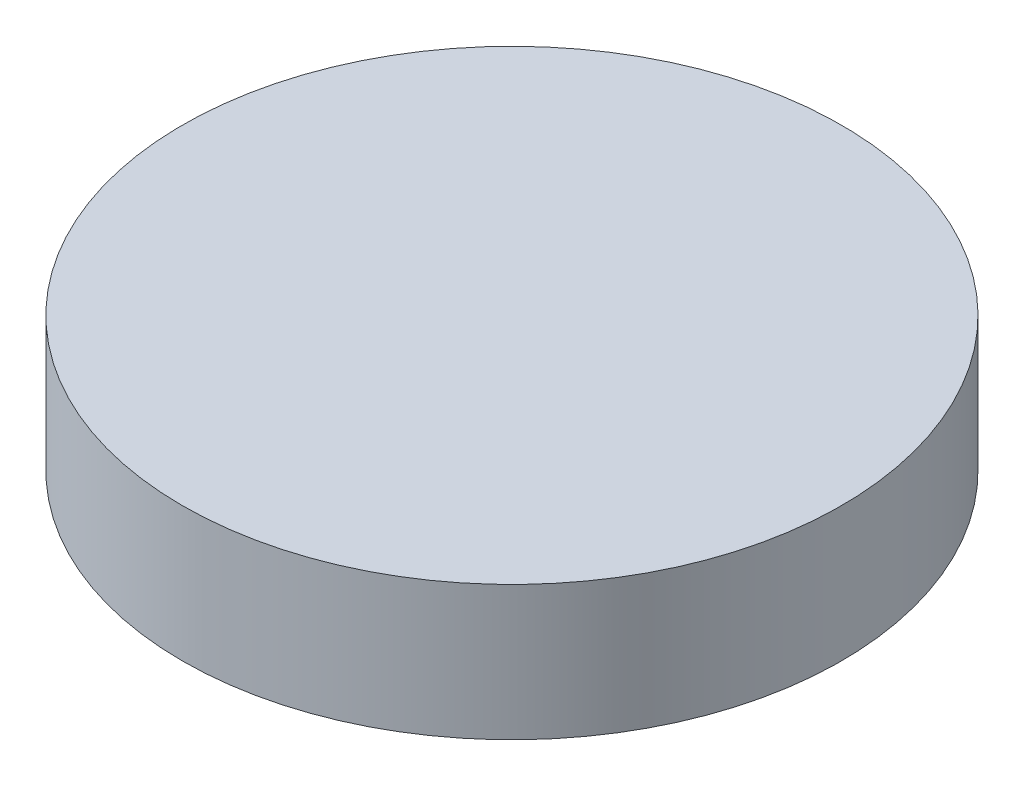
SolidWorks part; units mm, degrees
ref_plane "Front" through (0, 0, 0) normal (0, 0, 1) x (1, 0, 0)
ref_plane "Top" through (0, 0, 0) normal (0, 1, 0) x (1, 0, 0)
ref_plane "Right" through (0, 0, 0) normal (1, 0, 0) x (0, 0, -1)
sketch "Çizim1" plane through (0, 0, 0) normal (0, 1, 0) x (1, 0, 0)
  circle A0 centre (-10.5923, -2.1804) radius 12.25
  dimension "D1" = 24.5
extrude "Yükseklik-Ekstrüzyon1" add sketch "Çizim1" along normal blind 5
